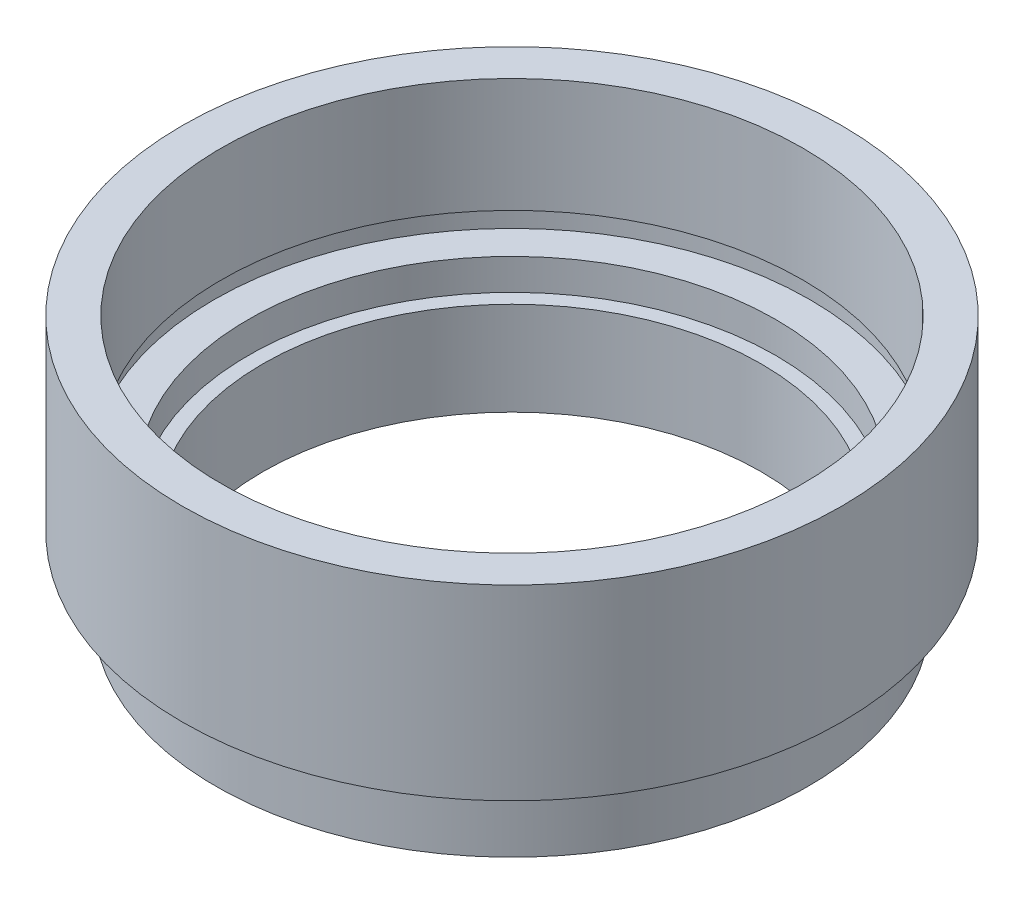
SolidWorks part; units mm, degrees
ref_plane "前视基准面" through (0, 0, 0) normal (0, 0, 1) x (1, 0, 0)
ref_plane "上视基准面" through (0, 0, 0) normal (0, 1, 0) x (1, 0, 0)
ref_plane "右视基准面" through (0, 0, 0) normal (1, 0, 0) x (0, 0, -1)
sketch "草图1" plane through (0, 0, 0) normal (0, 0, 1) x (1, 0, 0)
  line L0 (0, 0) -> (0, 21.8535) construction
  line L1 (12, 0) -> (14.25, 0)
  line L2 (14.25, 0) -> (14.25, 2.5)
  line L3 (14.25, 2.5) -> (13.75, 2.5)
  line L4 (13.75, 2.5) -> (13.75, 3.5)
  line L5 (13.75, 3.5) -> (15.875, 3.5)
  line L6 (15.875, 3.5) -> (15.875, 12.5)
  line L7 (15.875, 12.5) -> (14, 12.5)
  line L8 (14, 12.5) -> (14, 7)
  line L9 (14, 7) -> (14.35, 7)
  line L10 (14.35, 7) -> (14.35, 6)
  line L11 (14.35, 6) -> (12.7, 6)
  line L12 (12.7, 6) -> (12.7, 4.5)
  line L13 (12.7, 4.5) -> (12, 4.5)
  line L14 (12, 0) -> (12, 4.5)
  dimension "D1" = 12.5
  dimension "D2" = 15.875
  dimension "D3" = 14
  dimension "D4" = 12.7
  dimension "D5" = 1
  dimension "D6" = 1.5
  dimension "D7" = 12
  dimension "D8" = 14.25
  dimension "D9" = 1
  dimension "D10" = 3.5
  dimension "D11" = 4.5
  dimension "D12" = 14.35
  dimension "D13" = 13.75
revolve "旋转1" add sketch "草图1" angle 360 about L0
cosmetic thread "装饰螺纹线11" parameters "D2"=28
cosmetic thread "装饰螺纹线12" parameters "D2"=28.5
